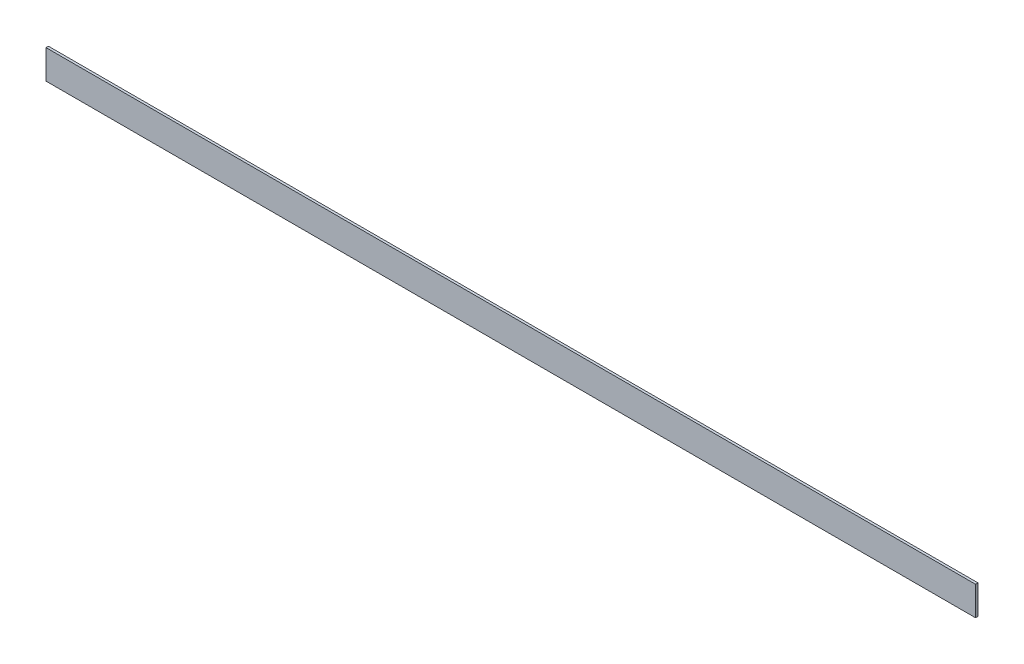
SolidWorks part; units mm, degrees
material "PVC 0.007 Plasticized"
ref_plane "Front Plane" through (0, 0, 0) normal (0, 0, 1) x (1, 0, 0)
ref_plane "Top Plane" through (0, 0, 0) normal (0, 1, 0) x (1, 0, 0)
ref_plane "Right Plane" through (0, 0, 0) normal (1, 0, 0) x (0, 0, -1)
sketch "Sketch1" plane through (0, 0, 0) normal (1, 0, 0) x (0, 0, -1)
  line L1 (-3.175, -38.1) -> (3.175, -38.1)
  line L2 (-3.175, -38.1) -> (-3.175, 38.1)
  line L3 (-3.175, 38.1) -> (3.175, 38.1)
  line L4 (3.175, -38.1) -> (3.175, 38.1)
  line L5 (-3.175, -38.1) -> (3.175, 38.1) construction
  line L6 (-3.175, 38.1) -> (3.175, -38.1) construction
  point P0 (0, 0)
  dimension "D1" = 76.2
  dimension "D2" = 6.35
extrude "Boss-Extrude1" add sketch "Sketch1" along normal blind 2438.4
equation "\"D2@Sketch1\"=1in/4"
